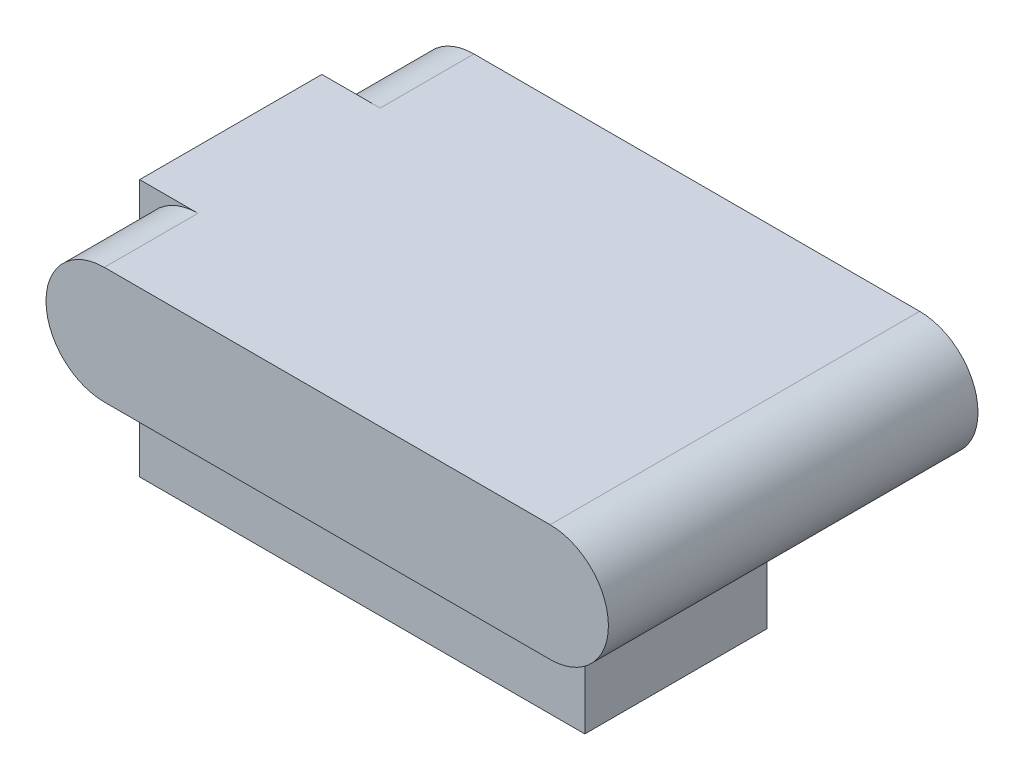
SolidWorks part; units mm, degrees
material "6061-T6 (SS)"
ref_plane "Front Plane" through (0, 0, 0) normal (0, 0, 1) x (1, 0, 0)
ref_plane "Top Plane" through (0, 0, 0) normal (0, 1, 0) x (1, 0, 0)
ref_plane "Right Plane" through (0, 0, 0) normal (1, 0, 0) x (0, 0, -1)
sketch "Sketch1" plane through (0, 0, 0) normal (0, 1, 0) x (1, 0, 0)
  line L1 (0, 0) -> (60.3758, 0)
  line L2 (0, 0) -> (0, 24.7142)
  line L3 (0, 24.7142) -> (60.3758, 24.7142)
  line L4 (60.3758, 0) -> (60.3758, 24.7142)
  dimension "D1" = 60.3758
  dimension "D2" = 24.7142
extrude "Boss-Extrude1" add sketch "Sketch1" along normal blind 34.925
sketch "Sketch2" plane through (0, 0, 0) normal (0, 0, 1) x (1, 0, 0)
  line L0 (0, 34.925) -> (60.3758, 34.925) construction
  line L1 (0, 34.925) -> (0, 0) construction
  line L3 (7.9121, 34.925) -> (68.3641, 34.925)
  line L5 (7.9121, 19.1008) -> (68.3641, 19.1008)
  arc A0 (7.9121, 34.925) -> (7.9121, 19.1008) centre (7.9121, 27.0129) ccw
  arc A1 (68.3641, 19.1008) -> (68.3641, 34.925) centre (68.3641, 27.0129) ccw
  dimension "D1" = 15.8242
  dimension "D2" = 60.452
extrude "Boss-Extrude2" add sketch "Sketch2" along normal blind 12.7 and the other way blind 37.4269
